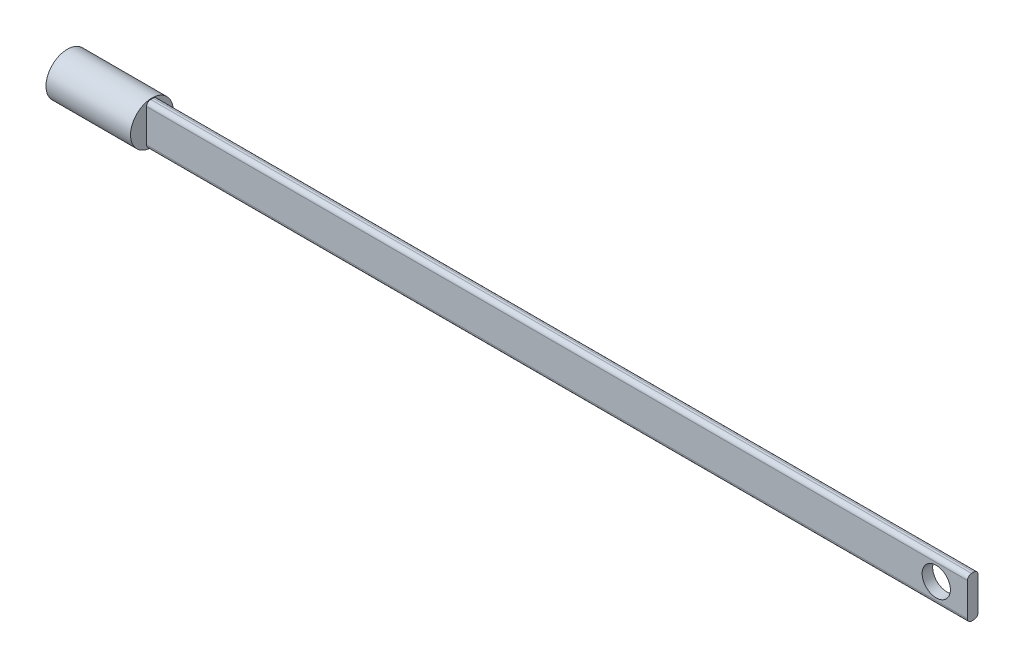
SolidWorks part; units mm, degrees
ref_plane "Front Plane" through (0, 0, 0) normal (0, 0, 1) x (1, 0, 0)
ref_plane "Top Plane" through (0, 0, 0) normal (0, 1, 0) x (1, 0, 0)
ref_plane "Right Plane" through (0, 0, 0) normal (1, 0, 0) x (0, 0, -1)
sketch "Sketch1" plane through (0, 0, 0) normal (1, 0, 0) x (0, 0, -1)
  circle A0 centre (0, 0) radius 6.604
extrude "Boss-Extrude1" add sketch "Sketch1" along normal blind 26.162
sketch "Sketch2" plane through (0, 0, 0) normal (-1, 0, 0) x (0, 0, 1)
  circle A0 centre (0, 0) radius 4.603
extrude "Cut-Extrude1" cut sketch "Sketch2" against normal blind 11.684
sketch "Sketch3" plane through (26.162, 0, 0) normal (1, 0, 0) x (0, 0, -1)
  line L1 (-1.6303, -6.3996) -> (1.6303, -6.3996)
  line L2 (-1.6303, -6.3996) -> (-1.6303, 6.3996)
  line L3 (-1.6303, 6.3996) -> (1.6303, 6.3996)
  line L4 (1.6303, -6.3996) -> (1.6303, 6.3996)
  line L5 (-1.6303, -6.3996) -> (1.6303, 6.3996) construction
  line L6 (-1.6303, 6.3996) -> (1.6303, -6.3996) construction
  circle A0 centre (0, 0) radius 6.604 construction
  point P0 (0, 0)
extrude "Boss-Extrude2" add sketch "Sketch3" along normal blind 254
fillet "Fillet2" radius 1.27 4 edges at (153.162, -6.3996, -1.6303) (153.162, 6.3996, -1.6303) (153.162, -6.3996, 1.6303) (153.162, 6.3996, 1.6303)
sketch "Sketch9" plane through (0, 0, 1.6303) normal (0, 0, 1) x (1, 0, 0)
  circle A0 centre (270.503, 0) radius 4.3688
extrude "Cut-Extrude4" cut sketch "Sketch9" against normal up to next
